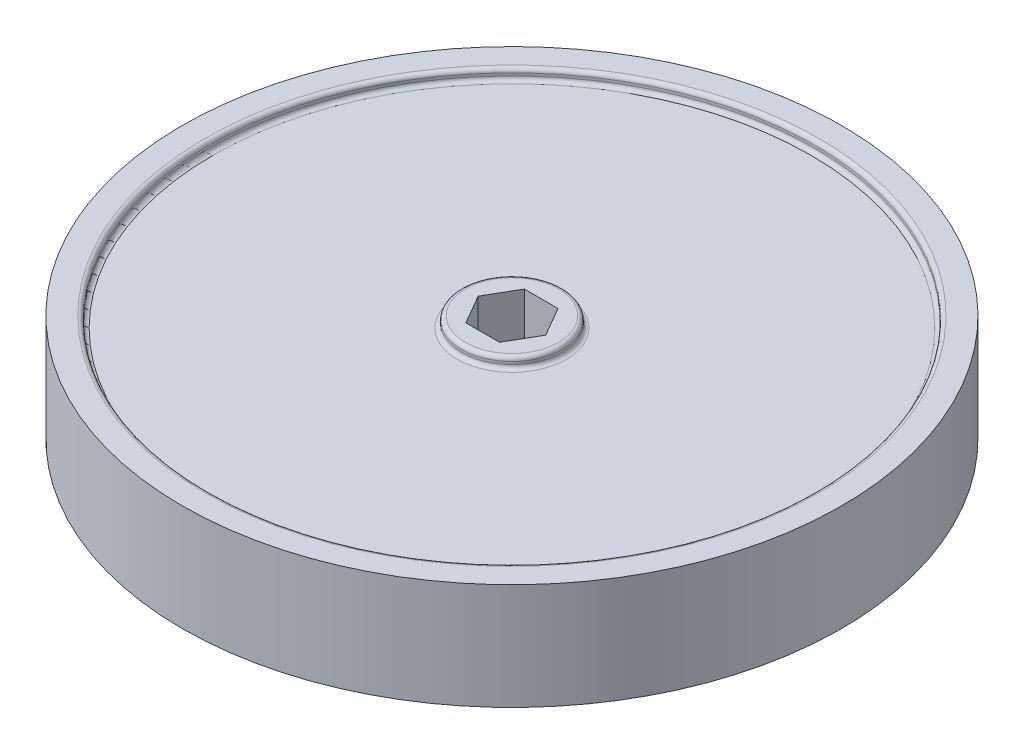
SolidWorks part; units mm, degrees
ref_plane "Piano frontale" through (0, 0, 0) normal (0, 0, 1) x (1, 0, 0)
ref_plane "Piano superiore" through (0, 0, 0) normal (0, 1, 0) x (1, 0, 0)
ref_plane "Piano destro" through (0, 0, 0) normal (1, 0, 0) x (0, 0, -1)
ref_plane "Piano1" through (0, 0, 0) normal (0, 0, -1) x (-1, 0, 0)
sketch "Schizzo1" plane through (0, 0, 0) normal (0, 0, -1) x (-1, 0, 0)
  line L0 (-62, -10) -> (0, -10)
  line L1 (0, -10) -> (0, 10)
  line L2 (0, 10) -> (-62, 10)
  line L3 (-62, 10) -> (-62, -10)
  line L4 (0, -10) -> (0, 10) construction
  dimension "D1" = 62
  dimension "D2" = 20
revolve "Rivoluzione1" add sketch "Schizzo1" angle 360 about L4
sketch "Schizzo9" plane through (0, -10, 0) normal (0, -1, 0) x (1, 0, 0)
  circle A0 centre (0, 0) radius 57
  circle A2 centre (0, 0) radius 62 construction
  dimension "D1" = 5
extrude "Taglio-Estrusione2" cut sketch "Schizzo9" against normal blind 2
sketch "Schizzo10" plane through (0, -8, 0) normal (0, -1, 0) x (1, 0, 0)
  circle A0 centre (0, 0) radius 9.5
  dimension "D1" = 19
extrude "Estrusione-Estrusione3" add sketch "Schizzo10" along normal blind 2
mirror "Specchia1" about plane through (0, 0, 0) normal (0, 1, 0) of "Estrusione-Estrusione3", "Taglio-Estrusione2"
sketch "Schizzo8" plane through (0, -8, 0) normal (0, 1, 0) x (-1, 0, 0)
  line L0 (-3.175, -5.4993) -> (3.175, -5.4993)
  line L1 (3.175, -5.4993) -> (6.35, 0)
  line L2 (6.35, 0) -> (3.175, 5.4993)
  line L3 (3.175, 5.4993) -> (-3.175, 5.4993)
  line L4 (-3.175, 5.4993) -> (-6.35, 0)
  line L5 (-6.35, 0) -> (-3.175, -5.4993)
extrude "Taglio-Estrusione1" cut sketch "Schizzo8" against normal through all and the other way through all
fillet "Raccordo1" radius 0.75 7 edges at (0, -8, -57) (0, 10, -57) (0, 8, -57) (0, 8, 9.5) (0, 10, -9.5) (0, -10, -9.5) (0, -10, -57)
